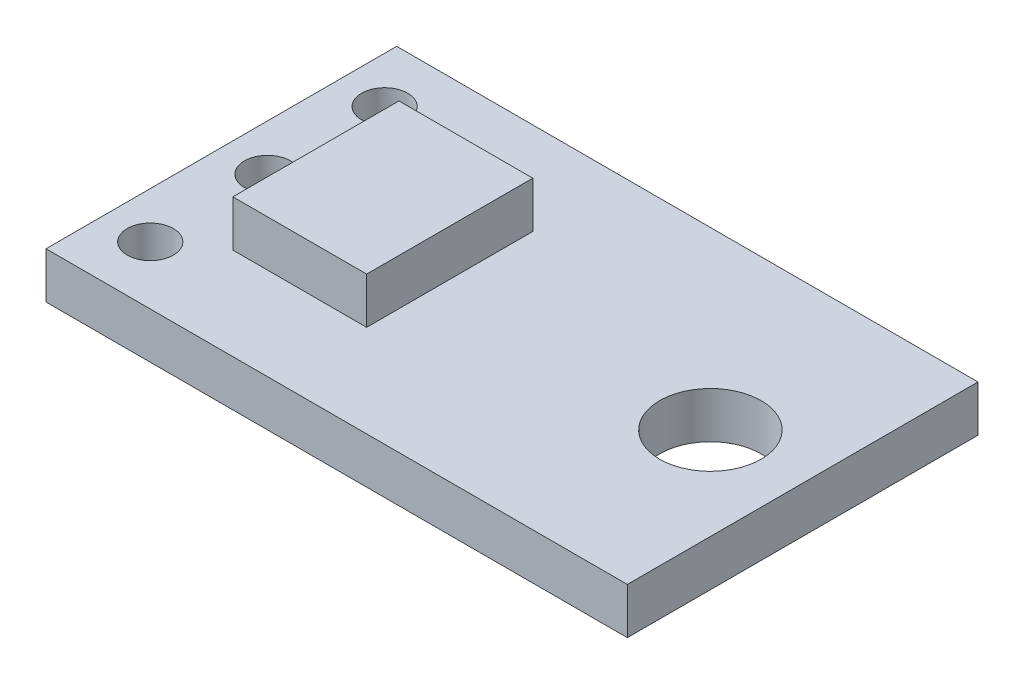
SolidWorks part; units mm, degrees
ref_plane "Ön Düzlem" through (0, 0, 0) normal (0, 0, 1) x (1, 0, 0)
ref_plane "Üst Düzlem" through (0, 0, 0) normal (0, 1, 0) x (1, 0, 0)
ref_plane "Sağ Düzlem" through (0, 0, 0) normal (1, 0, 0) x (0, 0, -1)
sketch "Sketch1" plane through (0, 0, 0) normal (0, 1, 0) x (1, 0, 0)
  line L1 (-24.5, 18.3841) -> (-7.5, 18.3841)
  line L2 (-24.5, 18.3841) -> (-24.5, 8.3841)
  line L3 (-24.5, 8.3841) -> (-7.5, 8.3841)
  line L4 (-7.5, 18.3841) -> (-7.5, 8.3841)
  dimension "D1" = 17
  dimension "D2" = 10
extrude "Boss-Extrude1" add sketch "Sketch1" along normal blind 1
sketch "Sketch2" plane through (0, 1, 0) normal (0, 1, 0) x (1, 0, 0)
  line L0 (-7.5, 18.3841) -> (-24.5, 18.3841) construction
  line L1 (-22.5, 11.3841) -> (-19.5, 11.3841)
  line L2 (-22.5, 11.3841) -> (-22.5, 15.3841)
  line L3 (-22.5, 15.3841) -> (-19.5, 15.3841)
  line L4 (-19.5, 11.3841) -> (-19.5, 15.3841)
  line L5 (-24.5, 8.3841) -> (-7.5, 8.3841) construction
  line L6 (-24.5, 18.3841) -> (-24.5, 8.3841) construction
  dimension "D1" = 3
  dimension "D2" = 3
  dimension "D3" = 2
  dimension "D4" = 3
extrude "Boss-Extrude2" add sketch "Sketch2" along normal blind 1
sketch "Sketch3" plane through (0, 1, 0) normal (0, 1, 0) x (1, 0, 0)
  line L0 (-24.5, 9.5841) -> (-24.5, 17.1841)
  line L1 (-24.5, 18.3841) -> (-24.5, 8.3841) construction
  line L2 (-24.5, 17.1841) -> (-11.9, 17.1841)
  line L3 (-11.9, 17.1841) -> (-11.9, 9.5841)
  line L4 (-11.9, 9.5841) -> (-24.5, 9.5841)
  line L6 (-29.1811, 19.334) -> (-6.8726, 19.334)
  line L7 (-29.1811, 19.334) -> (-29.1811, 7.8528)
  line L8 (-29.1811, 7.8528) -> (-6.8726, 7.8528)
  line L9 (-6.8726, 19.334) -> (-6.8726, 7.8528)
  dimension "D1" = 7.6
  dimension "D2" = 7.6
  dimension "D3" = 12.6
  dimension "D4" = 1.2
  dimension "D5" = 1.2
extrude "Cut-Extrude1" cut sketch "Sketch3" against normal blind 1
sketch "Sketch4" plane through (0, 1, 0) normal (0, 1, 0) x (1, 0, 0)
  line L0 (-24.5, 17.1841) -> (-24.5, 9.5841) construction
  line L2 (-11.9, 9.5841) -> (-11.9, 17.1841) construction
  circle A0 centre (-23.5, 13.3841) radius 0.5
  circle A1 centre (-23.5, 15.9241) radius 0.5
  circle A2 centre (-23.5, 10.8441) radius 0.5
  circle A3 centre (-13.9, 13.3841) radius 1.1
  point P2 (-24.5, 13.3841)
  dimension "D1" = 1
  dimension "D3" = 2.54
  dimension "D5" = 2
  dimension "D2" = 3.8
  dimension "D4" = 2.54
extrude "Cut-Extrude2" cut sketch "Sketch4" against normal blind 1
sketch "Sketch5" plane through (0, 2, 0) normal (0, 1, 0) x (1, 0, 0)
  line L0 (-22.5, 15.3841) -> (-22.5, 11.3841) construction
  line L1 (-22.45, 15.1841) -> (-19.55, 15.1841)
  line L2 (-22.45, 15.1841) -> (-22.45, 11.5841)
  line L3 (-22.45, 11.5841) -> (-19.55, 11.5841)
  line L4 (-19.55, 15.1841) -> (-19.55, 11.5841)
  line L6 (-22.7494, 15.8918) -> (-19.1022, 15.8918)
  line L7 (-22.7494, 15.8918) -> (-22.7494, 11.0572)
  line L8 (-22.7494, 11.0572) -> (-19.1022, 11.0572)
  line L9 (-19.1022, 15.8918) -> (-19.1022, 11.0572)
  dimension "D1" = 2.9
  dimension "D2" = 0.05
  dimension "D3" = 3.6
  dimension "D4" = 0.2
extrude "Cut-Extrude3" cut sketch "Sketch5" against normal up to surface (1 mm away) up to face at (-13.9, 1, -12.2841)
